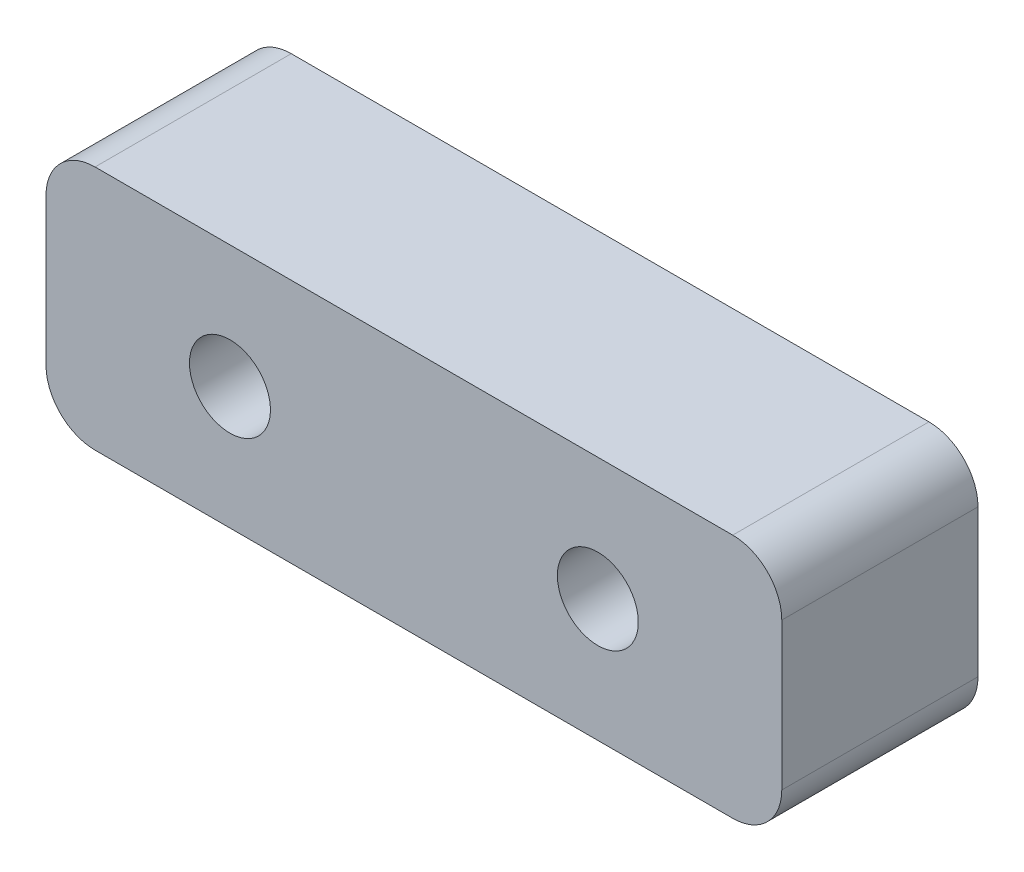
SolidWorks part; units mm, degrees
material "ABS"
ref_plane "前视基准面" through (0, 0, 0) normal (0, 0, 1) x (1, 0, 0)
ref_plane "上视基准面" through (0, 0, 0) normal (0, 1, 0) x (1, 0, 0)
ref_plane "右视基准面" through (0, 0, 0) normal (1, 0, 0) x (0, 0, -1)
other "Configuration Table"
sketch "草图1" plane through (0, 0, 0) normal (0, 0, 1) x (1, 0, 0)
  line L1 (-15, -5) -> (15, -5)
  line L2 (-15, -5) -> (-15, 5)
  line L3 (-15, 5) -> (15, 5)
  line L4 (15, -5) -> (15, 5)
  line L5 (-15, -5) -> (15, 5) construction
  line L6 (-15, 5) -> (15, -5) construction
  point P0 (0, 0)
  dimension "D1" = 10
  dimension "D2" = 30
extrude "凸台-拉伸1" add sketch "草图1" along normal blind 8
fillet "圆角1" radius 2 4 edges at (15, -5, 4) (-15, -5, 4) (15, 5, 4) (-15, 5, 4)
sketch "草图3" plane through (0, 0, 0) normal (0, 0, -1) x (-1, 0, 0)
  line L0 (0, 0) -> (0, 5) construction
  line L1 (-13, 5) -> (13, 5) construction
  circle A0 centre (-7.5, 0) radius 1.65
  circle A1 centre (7.5, 0) radius 1.65
  dimension "D1" = 3.3
  dimension "D2" = 15
extrude "切除-拉伸1" cut sketch "草图3" against normal through all
